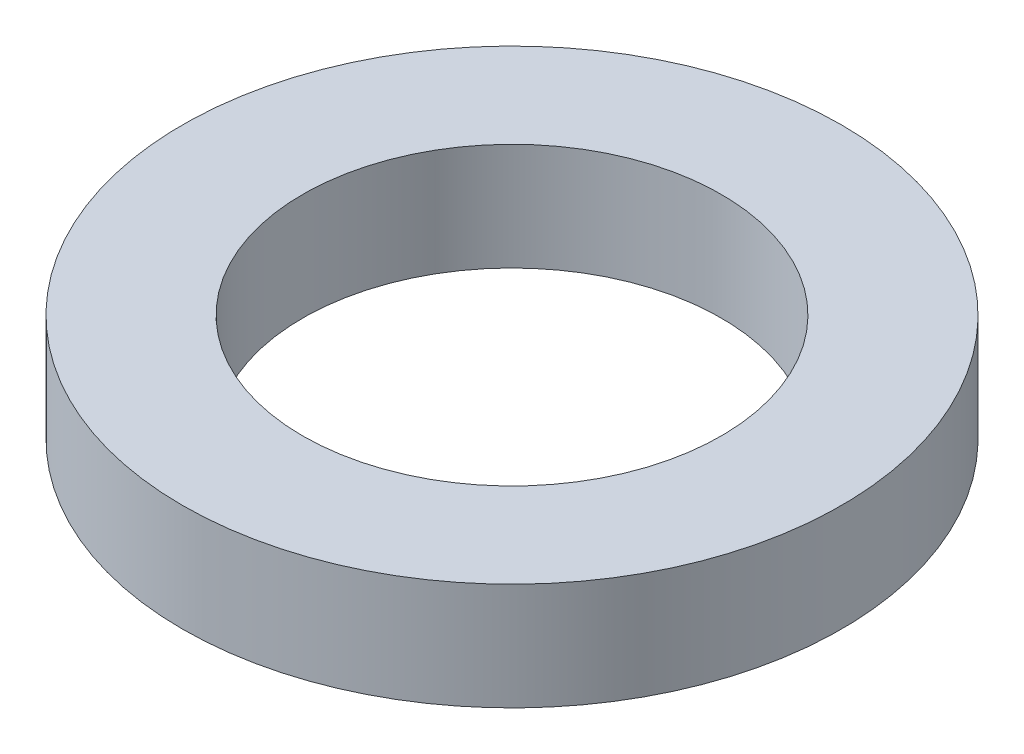
SolidWorks part; units mm, degrees
ref_plane "Front Plane" through (0, 0, 0) normal (0, 0, 1) x (1, 0, 0)
ref_plane "Top Plane" through (0, 0, 0) normal (0, 1, 0) x (1, 0, 0)
ref_plane "Right Plane" through (0, 0, 0) normal (1, 0, 0) x (0, 0, -1)
sketch "Sketch1" plane through (0, 0, 0) normal (0, 1, 0) x (1, 0, 0)
  circle A0 centre (0, 0) radius 1.5875
  circle A1 centre (0, 0) radius 2.5
  dimension "D1" = 3.175
  dimension "D2" = 5
extrude "Boss-Extrude1" add sketch "Sketch1" along normal blind 0.8128
